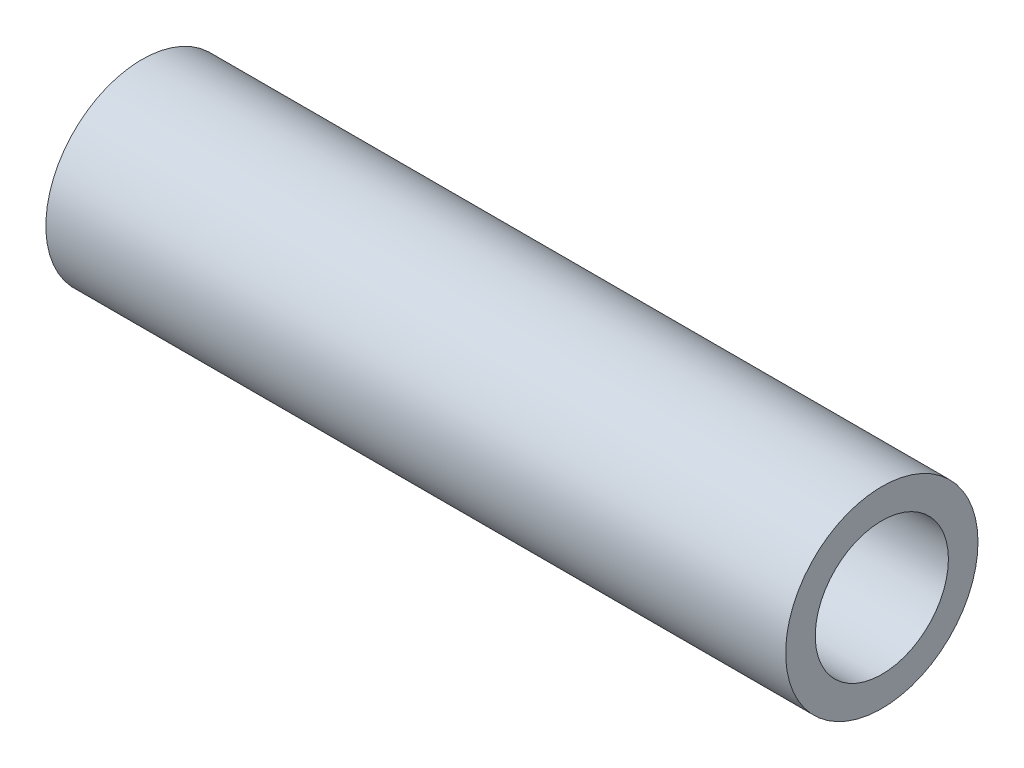
SolidWorks part; units mm, degrees
ref_plane "Спереди" through (0, 0, 0) normal (0, 0, 1) x (1, 0, 0)
ref_plane "Сверху" through (0, 0, 0) normal (0, 1, 0) x (1, 0, 0)
ref_plane "Справа" through (0, 0, 0) normal (1, 0, 0) x (0, 0, -1)
sketch "Эскиз1" plane through (0, 0, 0) normal (1, 0, 0) x (0, 0, -1)
  circle A0 centre (0, 0) radius 13
  circle A1 centre (0, 0) radius 9
  dimension "D1" = 26
  dimension "D2" = 18
extrude "Бобышка-Вытянуть1" add sketch "Эскиз1" along normal blind 100
